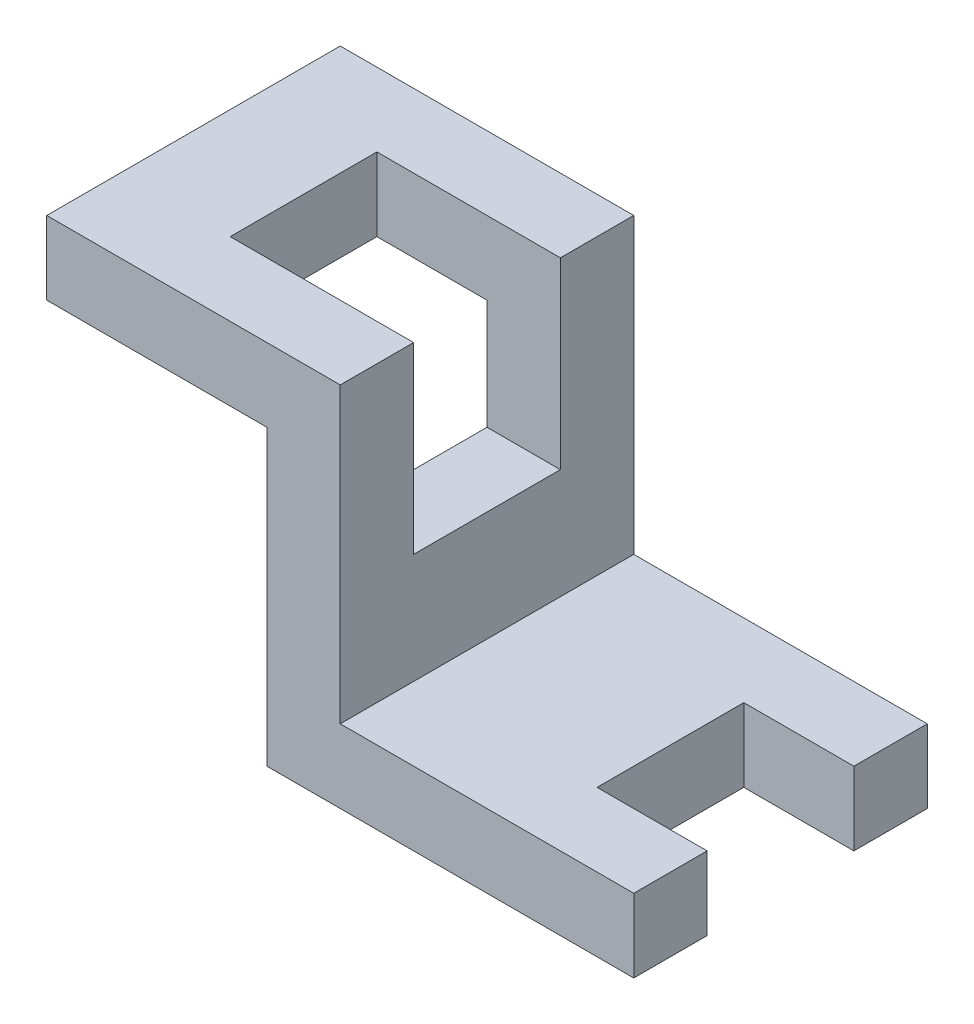
SolidWorks part; units mm, degrees
ref_plane "Front Plane" through (0, 0, 0) normal (0, 0, 1) x (1, 0, 0)
ref_plane "Top Plane" through (0, 0, 0) normal (0, 1, 0) x (1, 0, 0)
ref_plane "Right Plane" through (0, 0, 0) normal (1, 0, 0) x (0, 0, -1)
sketch "Sketch4" plane through (0, 0, 0) normal (0, 0, 1) x (1, 0, 0)
  line L0 (0, 0) -> (0, -10)
  line L1 (0, 0) -> (40, 0)
  line L2 (40, 0) -> (40, -40)
  line L3 (0, -10) -> (30, -10)
  line L4 (30, -10) -> (30, -50)
  line L5 (30, -50) -> (80, -50)
  line L6 (80, -50) -> (80, -40)
  line L7 (80, -40) -> (40, -40)
  point P10 (0, 0)
  dimension "D1" = 10
  dimension "D2" = 40
  dimension "D3" = 40
  dimension "D4" = 10
  dimension "D5" = 50
  dimension "D6" = 10
extrude "Boss-Extrude3" add sketch "Sketch4" along normal blind 40
sketch "Sketch5" plane through (0, 0, 0) normal (0, 1, 0) x (1, 0, 0)
  line L0 (40, -10) -> (15, -10)
  line L1 (40, -40) -> (40, 0) construction
  line L2 (15, -10) -> (15, -30)
  line L3 (15, -30) -> (40, -30)
  line L4 (0, -40) -> (0, 0) construction
  line L5 (40, 0) -> (0, 0) construction
  line L6 (40, -40) -> (0, -40) construction
  dimension "D1" = 15
  dimension "D2" = 10
  dimension "D3" = 10
extrude "Cut-Extrude1" cut sketch "Sketch5" against normal blind 25 and the other way through all
sketch "Sketch6" plane through (0, -40, 0) normal (0, 1, 0) x (1, 0, 0)
  line L0 (80, -10) -> (65, -10)
  line L1 (80, -40) -> (80, 0) construction
  line L2 (65, -10) -> (65, -30)
  line L3 (65, -30) -> (80, -30)
  line L4 (80, 0) -> (40, 0) construction
  line L5 (80, -40) -> (40, -40) construction
  dimension "D1" = 10
  dimension "D2" = 10
  dimension "D3" = 15
extrude "Cut-Extrude2" cut sketch "Sketch6" against normal through all
